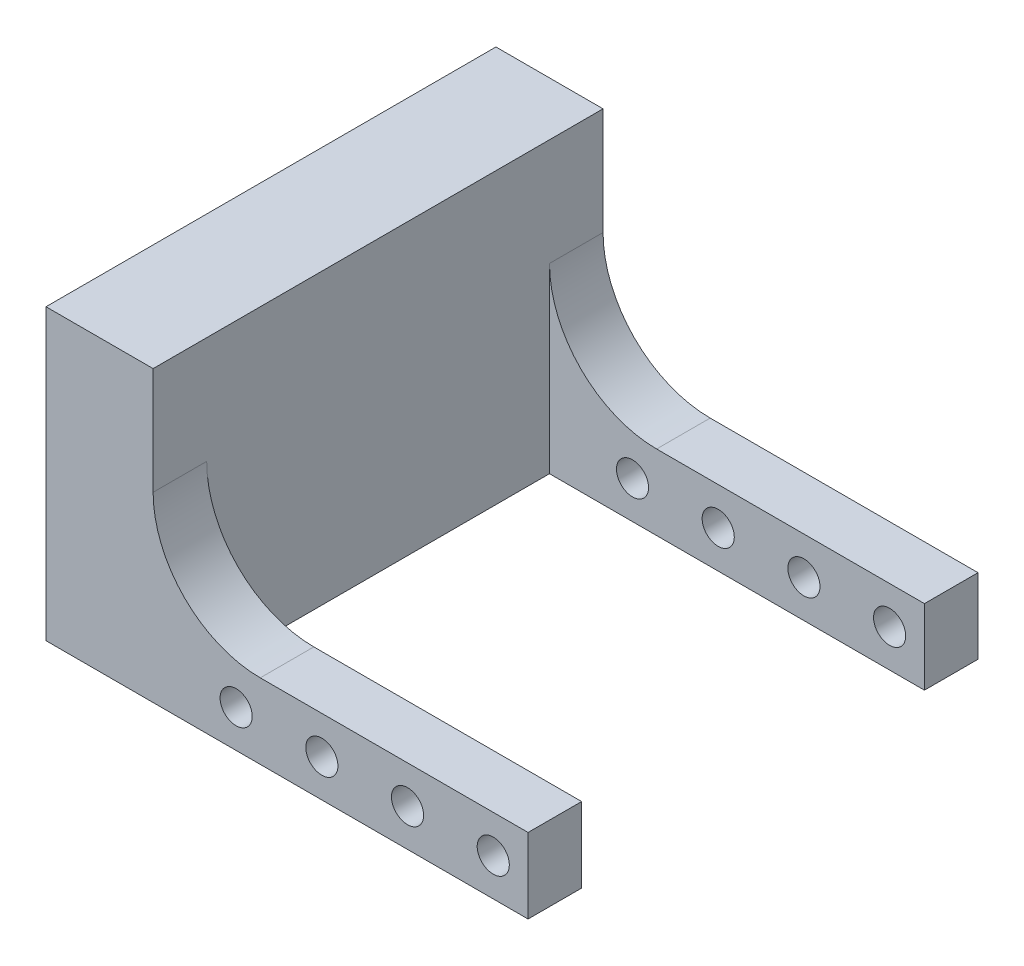
SolidWorks part; units mm, degrees
ref_plane "Plan de face" through (0, 0, 0) normal (0, 0, 1) x (1, 0, 0)
ref_plane "Plan de dessus" through (0, 0, 0) normal (0, 1, 0) x (1, 0, 0)
ref_plane "Plan de droite" through (0, 0, 0) normal (1, 0, 0) x (0, 0, -1)
sketch "Esquisse1" plane through (0, 0, 0) normal (0, 0, 1) x (1, 0, 0)
  line L0 (0, 7) -> (0, 27)
  line L1 (0, 0) -> (35, 0)
  line L2 (0, 0) -> (0, 7) construction
  line L3 (0, 7) -> (35, 7)
  line L4 (35, 0) -> (35, 7)
  line L5 (0, 0) -> (-10, 0)
  line L6 (0, 0) -> (0, 27) construction
  line L7 (0, 27) -> (-10, 27)
  line L8 (-10, 0) -> (-10, 27)
extrude "Boss.-Extru.1" add sketch "Esquisse1" along normal blind 42
sketch "Esquisse2" plane through (0, 0, 42) normal (0, 0, 1) x (1, 0, 0)
  line L0 (35, 3.5) -> (2.651, 3.5) construction
  line L1 (35, 0) -> (35, 7) construction
  line L2 (-10, 0) -> (35, 0) construction
  circle A0 centre (31.75, 3.5) radius 1.5
  circle A1 centre (23.75, 3.5) radius 1.5
  circle A2 centre (15.75, 3.5) radius 1.5
  circle A3 centre (7.75, 3.5) radius 1.5
  point P9 (0, 0)
sketch "Esquisse3" plane through (0, 7, 0) normal (0, 1, 0) x (1, 0, 0)
  line L0 (35, -42) -> (35, 0) construction
  line L1 (35, -37) -> (0, -37)
  line L2 (35, -37) -> (35, -5)
  line L3 (35, -5) -> (0, -5)
  line L4 (0, -37) -> (0, -5)
  line L5 (0, -42) -> (0, 0) construction
  line L6 (35, -42) -> (35, -37) construction
  line L7 (35, -5) -> (35, 0) construction
extrude "Enlèv. mat.-Extru.2" cut sketch "Esquisse3" against normal through all
extrude "Enlèv. mat.-Extru.3" cut sketch "Esquisse2" against normal through all
fillet "Congé1" radius 10 2 edges at (0, 7, 2.5) (0, 7, 39.5)
